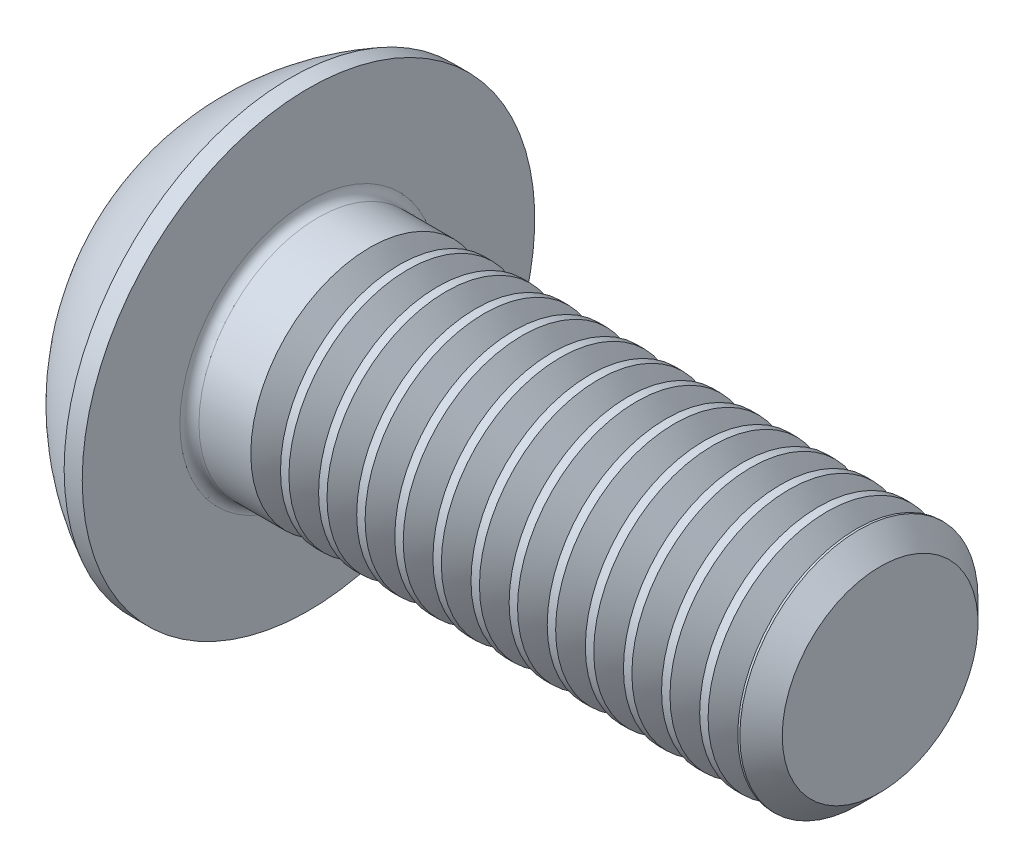
SolidWorks part; units mm, degrees
ref_plane "Plane1" through (0, 0, 0) normal (0, 0, 1) x (1, 0, 0)
ref_plane "Plane2" through (0, 0, 0) normal (0, 1, 0) x (1, 0, 0)
ref_plane "Plane3" through (0, 0, 0) normal (1, 0, 0) x (0, 0, -1)
sketch "BodySke" plane through (0, 0, 0) normal (0, 0, 1) x (1, 0, 0)
  line L0 (14.75, 0) -> (14.75, 2.055)
  line L1 (14.305, 2.5) -> (2.75, 2.5)
  line L2 (2.75, 2.5) -> (2.75, 4.75)
  line L3 (2.75, 4.75) -> (2.37, 4.75)
  line L4 (0, 0) -> (101.6, 0) construction
  line L5 (2.75, -4.75) -> (2.37, -4.75) construction
  line L6 (55.6768, -2.5) -> (2.75, -2.5) construction
  line L7 (14.75, 0) -> (0, 0)
  line L8 (0, 2.375) -> (0, -2.375) construction
  line L9 (0, 0) -> (0, 2.375)
  line L10 (14.75, 2.055) -> (14.305, 2.5)
  line L11 (14.75, -2.055) -> (14.305, -2.5) construction
  line L12 (3.55, 9.525) -> (3.55, -2.5) construction
  line L13 (2.75, 9.525) -> (2.75, -2.5) construction
  arc A1 (0, 2.375) -> (2.37, 4.75) centre (4.755, 0) cw
  dimension "Diameter" = 5
  dimension "Length" = 12
  dimension "Head_dia" = 9.5
  dimension "D1" = 4.75
  dimension "Head_ht" = 2.75
  dimension "Head_side_ht" = 0.38
  dimension "Minor_dia" = 4.11
  dimension "Body_ch_ang" = 45
  dimension "Advance" = 0.8
  dimension "Thread_nom" = 12
revolve "BaseBody" add sketch "BodySke" angle 360 about L4
cosmetic thread "ThreadCosmetic" [suppressed] parameters "Thread_length"=10.4, "Thread_minor"=4.11
fillet "Fillet1" radius 0.2 1 edges at (2.75, 0, 2.5)
sketch "Sketch2" plane through (0, 0, 0) normal (0, 0, 1) x (1, 0, 0)
  line L0 (0, 1.5) -> (1.56, 1.5)
  line L1 (1.56, 1.5) -> (2.426, 0)
  line L3 (2.426, 0) -> (0, 0)
  line L4 (0, 0) -> (0, 1.5)
  line L5 (0, -1.5) -> (1.56, -1.5) construction
  line L6 (0, 0) -> (47.625, 0) construction
  dimension "D2" = 60
  dimension "PreBroach_depth" = 1.56
  dimension "PreBroach_dia" = 3
revolve "PreBroach" cut sketch "Sketch2" angle 360 about L6
sketch "Sketch3" plane through (0, 0, 0) normal (1, 0, 0) x (0, 0, -1)
  line L0 (-1.5, -0.866) -> (-1.5, 0.866)
  line L1 (-1.5, 0.866) -> (0, 1.7321)
  line L2 (0, 1.7321) -> (1.5, 0.866)
  line L3 (1.5, 0.866) -> (1.5, -0.866)
  line L4 (1.5, -0.866) -> (0, -1.7321)
  line L5 (0, -1.7321) -> (-1.5, -0.866)
  dimension "Hex_size" = 3
  dimension "D3" = 3
  dimension "D1" = 1.5
  dimension "D2" = 1.5
extrude "Hex" cut sketch "Sketch3" along normal blind 1.56
sketch "ThdSchSke" plane through (0, 0, 0) normal (0, 0, 1) x (1, 0, 0)
  line L0 (4.35, -2.055) -> (4.0384, -2.5)
  line L1 (4.35, -2.055) -> (4.6616, -2.5)
  line L2 (4.6616, -2.5) -> (4.6616, -3.125)
  line L3 (-3.175, 0) -> (5.1513, 0) construction
  line L5 (4.6616, -3.125) -> (4.0384, -3.125)
  line L6 (4.0384, -3.125) -> (4.0384, -2.5)
  dimension "Diameter" = 5
  dimension "Thread_minor" = 4.11
  dimension "SideAngle" = 55
  dimension "VeeAngle" = 70
  dimension "Overcut" = 6.25
  dimension "Start" = 4.35
revolve "ThreadSchematic" cut sketch "ThdSchSke" angle 360 about L3
pattern_linear "ThdSchPat" count 13 spacing 0.8 along (1, 0, 0) of "ThreadSchematic"
equation "\"D1@BodySke\" = \"Head_dia@BodySke\" * .5"
equation "\"Thread_minor@ThreadCosmetic\" = \"Minor_dia@BodySke\""
equation "\"D1@Sketch3\" = \"Hex_size@Sketch3\" / 2"
equation "\"D2@Sketch3\" = \"D1@Sketch3\""
equation "\"D3@Sketch3\" = \"Hex_size@Sketch3\""
equation "\"Thread_length@ThreadCosmetic\" = ((sgn( (\"Length@BodySke\" - \"Advance@BodySke\" * 2.0) - \"Thread_nom@BodySke\" )-1)*( (\"Length@BodySke\" - \"Advance@BodySke\" * 2.0) - \"Thread_nom@BodySke\" ))/-2+ \"Thread_nom@BodySke\""
equation "\"Thread_minor@ThdSchSke\" = \"Minor_dia@BodySke\""
equation "\"Diameter@ThdSchSke\" = \"Diameter@BodySke\""
equation "\"Overcut@ThdSchSke\" = \"Diameter@BodySke\" * 1.25"
equation "\"Start@ThdSchSke\" = \"Head_ht@BodySke\" + \"Length@BodySke\" - \"Thread_length@ThreadCosmetic\"  '---Non-countersunk---"
equation "\"Num_threads@ThdSchPat\" = int( \"Thread_length@ThreadCosmetic\" / \"Advance@BodySke\" + 0.999 )  + 1"
equation "\"Advance@ThdSchPat\" = \"Thread_length@ThreadCosmetic\" /  (\"Num_threads@ThdSchPat\" - 1) 'relax it"
equation "\"Num_threads@ThdSchPat\" = \"Num_threads@ThdSchPat\" - sgn( \"Num_threads@ThdSchPat\" - 1) '---chamfered tips only---"
